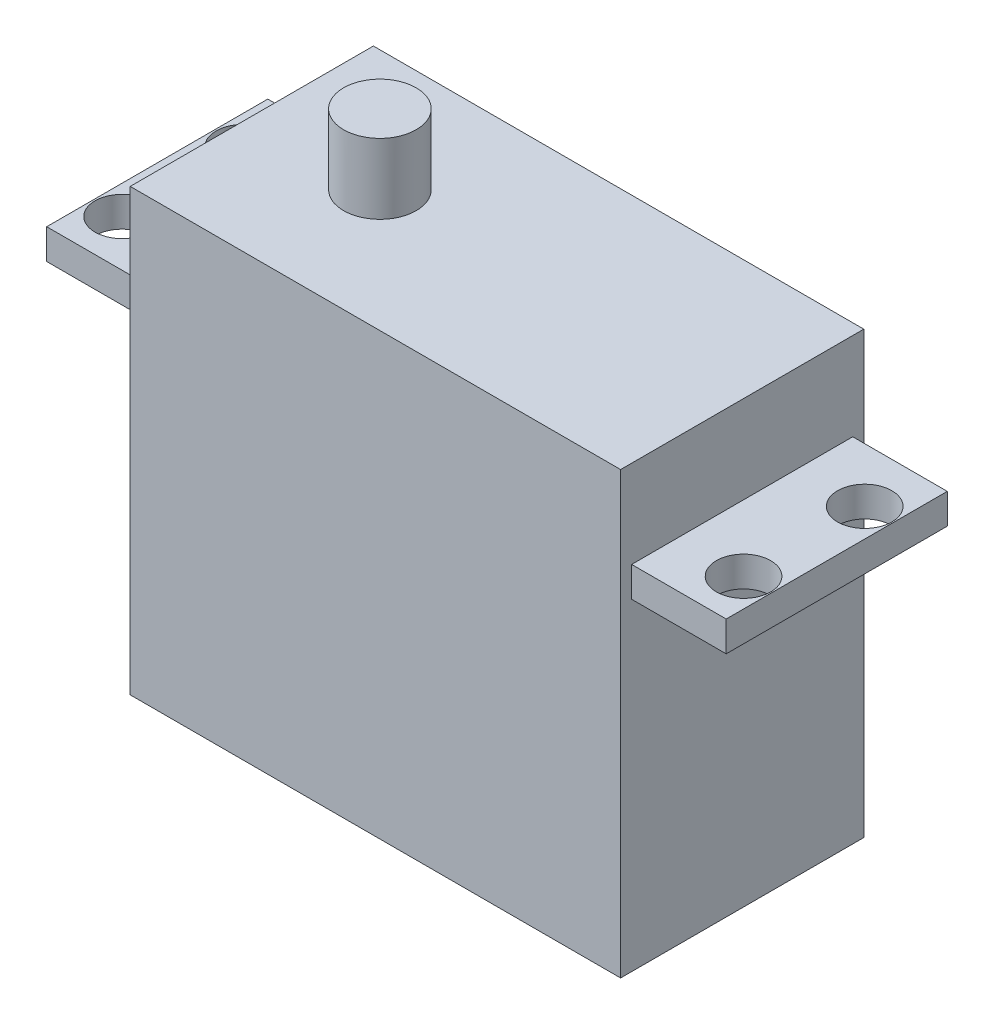
SolidWorks part; units mm, degrees
ref_plane "Front Plane" through (0, 0, 0) normal (0, 0, 1) x (1, 0, 0)
ref_plane "Top Plane" through (0, 0, 0) normal (0, 1, 0) x (1, 0, 0)
ref_plane "Right Plane" through (0, 0, 0) normal (1, 0, 0) x (0, 0, -1)
sketch "Sketch1" plane through (0, 0, 0) normal (0, 0, 1) x (1, 0, 0)
  line L1 (0, 0) -> (-55.499, 0)
  line L2 (0, 0) -> (0, -35.9664)
  line L3 (0, -35.9664) -> (-55.499, -35.9664)
  line L4 (-55.499, 0) -> (-55.499, -35.9664)
  dimension "D1" = 55.499
  dimension "D2" = 35.9664
extrude "Boss-Extrude1" add sketch "Sketch1" along normal blind 19.8628
sketch "Sketch2" plane through (0, 0, 19.8628) normal (0, 0, 1) x (1, 0, 0)
  line L0 (-55.499, -35.9664) -> (0, -35.9664) construction
  line L1 (-55.499, 0) -> (-47.7774, 0)
  line L2 (-55.499, 0) -> (-55.499, -7.1628)
  line L3 (-55.499, -7.1628) -> (-47.7774, -7.1628)
  line L4 (-47.7774, 0) -> (-47.7774, -7.1628)
  line L5 (-55.499, -9.6266) -> (-47.7774, -9.6266)
  line L6 (-55.499, -9.6266) -> (-55.499, -35.9664)
  line L7 (-55.499, -35.9664) -> (-47.7774, -35.9664)
  line L8 (-47.7774, -9.6266) -> (-47.7774, -35.9664)
  line L9 (-55.499, 0) -> (-55.499, -35.9664) construction
  line L10 (0, 0) -> (-55.499, 0) construction
  dimension "D1" = 7.7216
  dimension "D2" = 26.3398
  dimension "D3" = 7.1628
  dimension "D4" = 7.7216
extrude "Cut-Extrude1" cut sketch "Sketch2" against normal up to surface (19.8628 mm away) up to face at (-27.7495, -17.9832, 0)
sketch "Sketch3" plane through (0, 0, 19.8628) normal (0, 0, 1) x (1, 0, 0)
  line L0 (-47.7774, -35.9664) -> (0, -35.9664) construction
  line L1 (-7.7216, 0) -> (0, 0)
  line L2 (-7.7216, 0) -> (-7.7216, -7.1628)
  line L3 (-7.7216, -7.1628) -> (0, -7.1628)
  line L4 (0, 0) -> (0, -7.1628)
  line L5 (-7.7216, -9.6266) -> (0, -9.6266)
  line L6 (-7.7216, -9.6266) -> (-7.7216, -35.9664)
  line L7 (-7.7216, -35.9664) -> (0, -35.9664)
  line L8 (0, -9.6266) -> (0, -35.9664)
  line L9 (0, -35.9664) -> (0, 0) construction
  line L10 (-47.7774, -9.6266) -> (-55.499, -9.6266) construction
  line L11 (0, 0) -> (-47.7774, 0) construction
  line L12 (-55.499, -7.1628) -> (-47.7774, -7.1628) construction
  dimension "D1" = 7.7216
  dimension "D2" = 0
  dimension "D3" = 0
  dimension "D4" = 0
extrude "Cut-Extrude2" cut sketch "Sketch3" against normal up to surface (19.8628 mm away) up to face at (-37.7634, -13.189, 0)
sketch "Sketch4" plane through (0, -7.1628, 0) normal (0, 1, 0) x (1, 0, 0)
  line L0 (-50.927, -5.2641) -> (-50.927, -3.048) construction
  line L1 (-55.499, 0) -> (-55.499, -19.8628) construction
  line L2 (-53.1431, -3.048) -> (-55.499, -3.048) construction
  line L3 (-55.499, 0) -> (-47.7774, 0) construction
  line L4 (-53.1431, -12.9413) -> (-54.9503, -12.9413) construction
  line L5 (-50.927, -15.1574) -> (-50.927, -12.9413) construction
  line L6 (-53.1431, -7.4803) -> (-54.9503, -7.4803) construction
  line L7 (-0.0986, -5.3345) -> (-0.0986, -3.1183) construction
  line L8 (-2.3147, -3.1183) -> (-6.9853, -3.1183) construction
  line L9 (-2.3147, -13.0116) -> (-4.1219, -13.0116) construction
  line L10 (-0.0986, -15.2278) -> (-0.0986, -13.0116) construction
  line L11 (-2.3147, -7.5506) -> (-4.1219, -7.5506) construction
  line L12 (-7.7216, 0) -> (0, 0) construction
  line L13 (0, 0) -> (0, -19.8628) construction
  circle A0 centre (-53.1431, -5.2641) radius 2.2162
  circle A1 centre (-53.1431, -15.1574) radius 2.2162
  circle A2 centre (-2.3147, -5.3345) radius 2.2162
  circle A3 centre (-2.3147, -15.2278) radius 2.2162
  dimension "D1" = 4.4323
  dimension "D4" = 4.4323
  dimension "D7" = 4.4323
  dimension "D8" = 4.4323
  dimension "D11" = 2.3147
  dimension "D12" = 2.3147
  dimension "D2" = 4.572
  dimension "D3" = 3.048
  dimension "D5" = 5.461
  dimension "D6" = 4.572
  dimension "D9" = 5.461
  dimension "D10" = 3.1183
extrude "Cut-Extrude3" cut sketch "Sketch4" against normal up to surface (2.4638 mm away) up to face at (-51.6382, -9.6266, 9.9314)
sketch "Sketch5" plane through (0, 0, 19.8628) normal (0, 0, 1) x (1, 0, 0)
  line L1 (-55.499, -7.1628) -> (-47.7774, -7.1628)
  line L2 (-55.499, -7.1628) -> (-55.499, -9.6266)
  line L3 (-55.499, -9.6266) -> (-47.7774, -9.6266)
  line L4 (-47.7774, -7.1628) -> (-47.7774, -9.6266)
  line L5 (-55.499, -7.1628) -> (-47.7774, -7.1628) construction
  line L6 (-55.499, -7.1628) -> (-55.499, -9.6266) construction
  line L7 (-47.7774, -9.6266) -> (-55.499, -9.6266) construction
extrude "Cut-Extrude4" cut sketch "Sketch5" against normal blind 0.9017
sketch "Sketch6" plane through (0, 0, 0) normal (0, 0, -1) x (-1, 0, 0)
  line L0 (55.499, -7.1628) -> (55.499, -9.6266) construction
  line L1 (47.7774, -7.1628) -> (55.499, -7.1628)
  line L2 (47.7774, -7.1628) -> (47.7774, -9.6266)
  line L3 (47.7774, -9.6266) -> (55.499, -9.6266)
  line L4 (55.499, -7.1628) -> (55.499, -9.6266)
  line L5 (47.7774, -9.6266) -> (55.499, -9.6266) construction
  line L6 (55.499, -7.1628) -> (47.7774, -7.1628) construction
extrude "Cut-Extrude5" cut sketch "Sketch6" against normal blind 0.9017
sketch "Sketch7" plane through (0, 0, 0) normal (0, 0, -1) x (-1, 0, 0)
  line L0 (0, -9.6266) -> (7.7216, -9.6266) construction
  line L1 (0, -7.1628) -> (7.7216, -7.1628)
  line L2 (0, -7.1628) -> (0, -9.6266)
  line L3 (0, -9.6266) -> (7.7216, -9.6266)
  line L4 (7.7216, -7.1628) -> (7.7216, -9.6266)
  line L5 (7.7216, -7.1628) -> (0, -7.1628) construction
  line L6 (0, -9.6266) -> (0, -7.1628) construction
extrude "Cut-Extrude6" cut sketch "Sketch7" against normal blind 0.9017
sketch "Sketch8" plane through (0, 0, 19.8628) normal (0, 0, 1) x (1, 0, 0)
  line L0 (0, -9.6266) -> (-7.7216, -9.6266) construction
  line L1 (-7.7216, -7.1628) -> (0, -7.1628)
  line L2 (-7.7216, -7.1628) -> (-7.7216, -9.6266)
  line L3 (-7.7216, -9.6266) -> (0, -9.6266)
  line L4 (0, -7.1628) -> (0, -9.6266)
  line L5 (-7.7216, -7.1628) -> (0, -7.1628) construction
  line L6 (0, -9.6266) -> (0, -7.1628) construction
extrude "Cut-Extrude7" cut sketch "Sketch8" against normal blind 0.9017
sketch "Sketch9" plane through (0, 0, 0) normal (0, 1, 0) x (1, 0, 0)
  line L0 (-37.3443, -6.9342) -> (-40.2282, -6.9342) construction
  line L1 (-7.7216, 0) -> (-47.7774, 0) construction
  line L2 (-40.3098, -9.8997) -> (-40.3098, -12.8651) construction
  line L3 (-47.7774, 0) -> (-47.7774, -19.8628) construction
  circle A0 centre (-37.3443, -9.8997) radius 2.9655
  dimension "D1" = 5.9309
  dimension "D2" = 6.9342
  dimension "D3" = 7.4676
extrude "Boss-Extrude2" add sketch "Sketch9" along normal blind 5.7277
